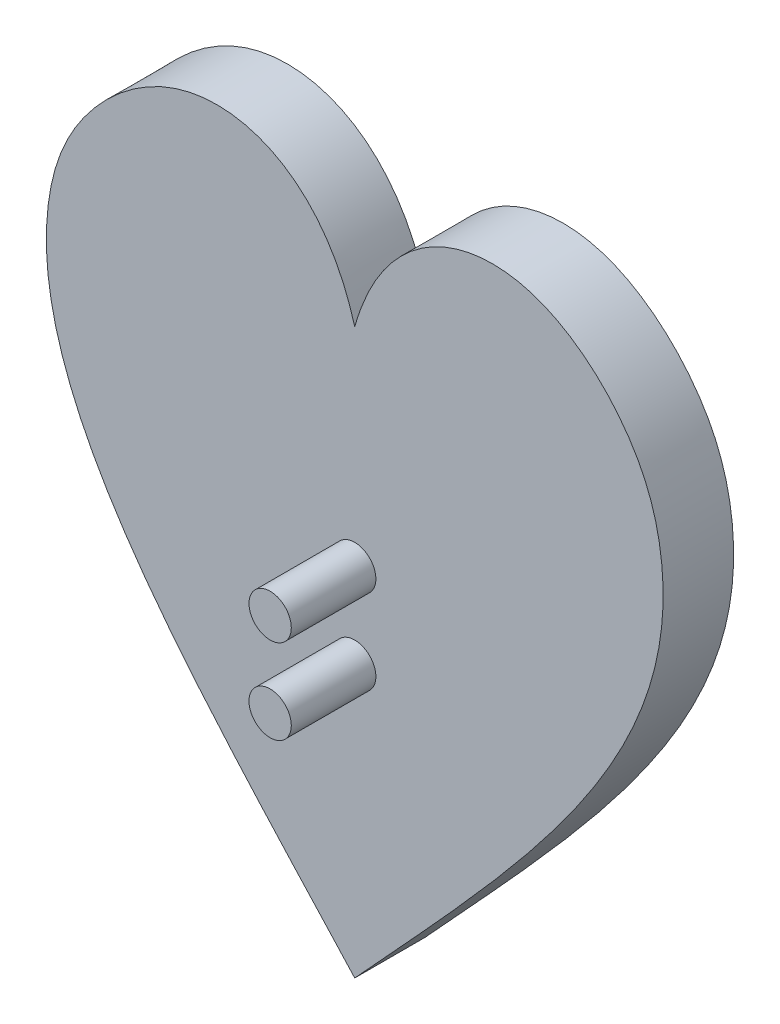
SolidWorks part; units mm, degrees
ref_plane "Front Plane" through (0, 0, 0) normal (0, 0, 1) x (1, 0, 0)
ref_plane "Top Plane" through (0, 0, 0) normal (0, 1, 0) x (1, 0, 0)
ref_plane "Right Plane" through (0, 0, 0) normal (1, 0, 0) x (0, 0, -1)
sketch "Sketch1" plane through (0, 0, 0) normal (0, 0, 1) x (1, 0, 0)
  line L0 (1.6546, 28.6371) -> (1.6546, -22.1629) construction
  spline S0 degree 3 poles (1.6546, 28.6371) (4.2709, 37.9946) (16.2802, 43.2489) (27.556, 32.3524) (32.8985, 10.5783) (16.6567, -5.7791) (1.6546, -22.1629) knots 0 0 0 0 0.212199 0.359774 0.438554 1 1 1 1
  spline S1 degree 3 poles (1.6546, 28.6371) (-0.9617, 37.9946) (-12.971, 43.2489) (-24.2468, 32.3524) (-29.5893, 10.5783) (-13.3475, -5.7791) (1.6546, -22.1629) knots 0 0 0 0 0.212199 0.359774 0.438554 1 1 1 1
  dimension "D1" = 50.8
extrude "Boss-Extrude1" add sketch "Sketch1" along normal blind 6.35
sketch "Sketch2" plane through (0, 0, 6.35) normal (0, 0, 1) x (1, 0, 0)
  line L0 (1.6546, 28.6371) -> (1.6546, -22.1629) construction
  circle A0 centre (1.6546, 9.9161) radius 1.905
  circle A1 centre (1.6546, 2.2961) radius 1.905
  dimension "D2" = 3.81
  dimension "D3" = 3.81
  dimension "D1" = 7.62
extrude "Boss-Extrude2" add sketch "Sketch2" along normal blind 7.62
